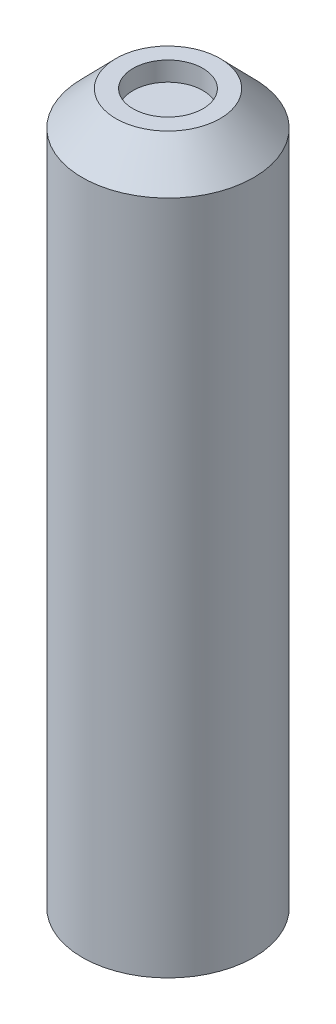
SolidWorks part; units mm, degrees
ref_plane "Front Plane" through (0, 0, 0) normal (0, 0, 1) x (1, 0, 0)
ref_plane "Top Plane" through (0, 0, 0) normal (0, 1, 0) x (1, 0, 0)
ref_plane "Right Plane" through (0, 0, 0) normal (1, 0, 0) x (0, 0, -1)
sketch "Sketch1" plane through (0, 0, 0) normal (0, 1, 0) x (1, 0, 0)
  circle A0 centre (0, 0) radius 12.5
  dimension "D1" = 25
extrude "Boss-Extrude1" add sketch "Sketch1" along normal blind 103.5
sketch "Sketch2" plane through (0, 0, 0) normal (1, 0, 0) x (0, 0, -1)
  line L1 (-12.5, 103.5) -> (-12.5, 0) construction
  line L3 (12.5, 103.5) -> (-12.5, 103.5) construction
  line L4 (-7.601, 103.5) -> (-12.5, 98.5)
  line L5 (-12.5, 98.5) -> (-12.5, 103.5)
  line L6 (-12.5, 103.5) -> (-7.601, 103.5)
  dimension "D1" = 5
  dimension "D2" = 7
ref_point "Point1"
ref_point "Point2"
ref_axis "Axis1" through (0, 0, 0) along (0, 1, 0)
revolve "Cut-Revolve4" cut sketch "Sketch2" angle 360 about axis through (0, 0, 0) along (0, 1, 0)
sketch "Sketch3" plane through (0, 103.5, 0) normal (0, 1, 0) x (1, 0, 0)
  circle A2 centre (0, 0) radius 5.101
  circle A3 centre (0, 0) radius 5.101
  dimension "D1" = 2.5
extrude "Cut-Extrude1" cut sketch "Sketch3" against normal blind 2.8
sketch "Sketch4" plane through (0, 0, 0) normal (0, -1, 0) x (1, 0, 0)
  circle A0 centre (0, 0) radius 4.25
  dimension "D1" = 8.5
extrude "Cut-Extrude2" cut sketch "Sketch4" against normal blind 9.5
